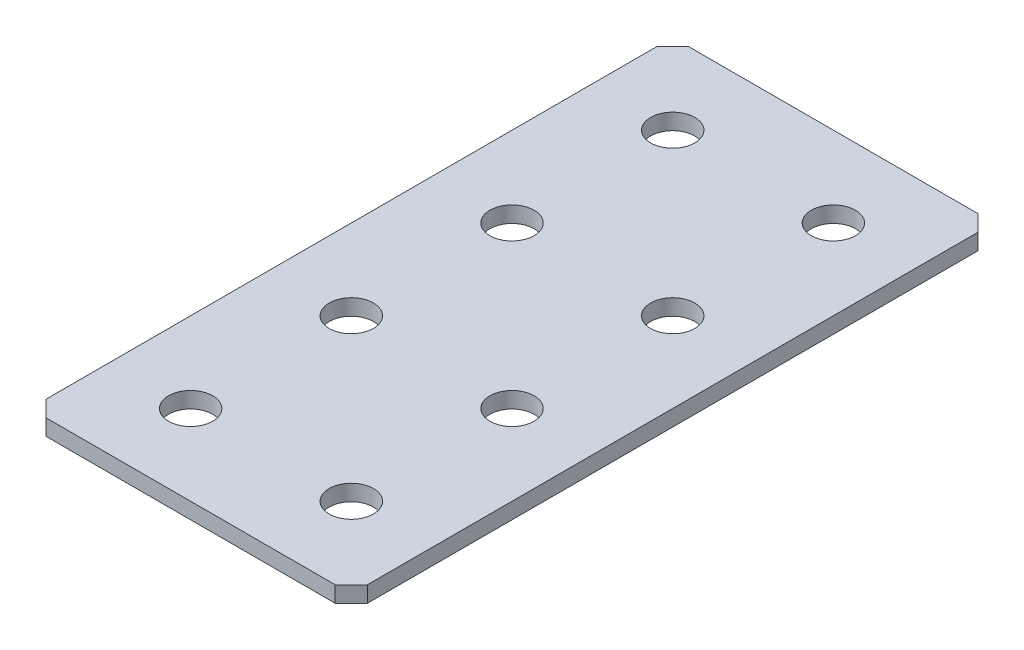
SolidWorks part; units mm, degrees
material "Простая углеродистая сталь"
ref_plane "Спереди(Плоскость XY)" through (0, 0, 0) normal (0, 0, 1) x (1, 0, 0)
ref_plane "Сверху(Плоскость XZ)" through (0, 0, 0) normal (0, 1, 0) x (1, 0, 0)
ref_plane "Справа(Плоскость ZY)" through (0, 0, 0) normal (1, 0, 0) x (0, 0, -1)
sketch "Эскиз1" plane through (0, 0, 0) normal (0, 1, 0) x (1, 0, 0)
  line L1 (-20, -40) -> (20, -40)
  line L2 (-20, -40) -> (-20, 40)
  line L3 (-20, 40) -> (20, 40)
  line L4 (20, -40) -> (20, 40)
  line L5 (-20, -40) -> (20, 40) construction
  line L6 (-20, 40) -> (20, -40) construction
  point P0 (0, 0)
  dimension "D1" = 40
  dimension "D2" = 80
extrude "Бобышка-Вытянуть1" add sketch "Эскиз1" along normal blind 2
chamfer "Фаска1" distance 2 angle 45 4 edges at (-20, 1, 40) (20, 1, 40) (-20, 1, -40) (20, 1, -40)
hole_wizard "Отверстие с зазором M51" positions "Эскиз2" profile "Эскиз3" hole size "M5" standard "DIN" end condition through all
sketch "Эскиз2" plane through (0, 2, 0) normal (0, 1, 0) x (1, 0, 0)
  line L2 (-10, 10) -> (10, 10) construction
  line L3 (-10, 10) -> (-10, 30) construction
  line L4 (-10, 30) -> (10, 30) construction
  line L5 (10, 10) -> (10, 30) construction
  line L7 (-10, -10) -> (10, -10) construction
  line L8 (-10, -10) -> (-10, -30) construction
  line L9 (-10, -30) -> (10, -30) construction
  line L10 (10, -10) -> (10, -30) construction
  line L11 (0, 10) -> (0, -10) construction
  point P0 (-10, 10)
  point P2 (10, 10)
  point P8 (-10, -10)
  point P10 (10, -10)
  point P22 (-10, 30)
  point P24 (10, 30)
  point P93 (10, -30)
  point P170 (-10, -30)
  dimension "D1" = 20
  dimension "D2" = 20
  dimension "D3" = 20
sketch "Эскиз3" plane through (-10, 2, -10) normal (1, 0, 0) x (0, 0, 1)
  line L0 (0, 0) -> (0, 2)
  line L1 (0, 2) -> (2.75, 2)
  line L2 (2.75, 2) -> (2.75, 0)
  line L5 (2.75, 0) -> (0, 0)
  line L11 (0, -6.35) -> (0, 107.95) construction
  dimension "Диаметр сквозного отверстия" = 5.5
  dimension "Глубина сквозного отверстия" = 2
